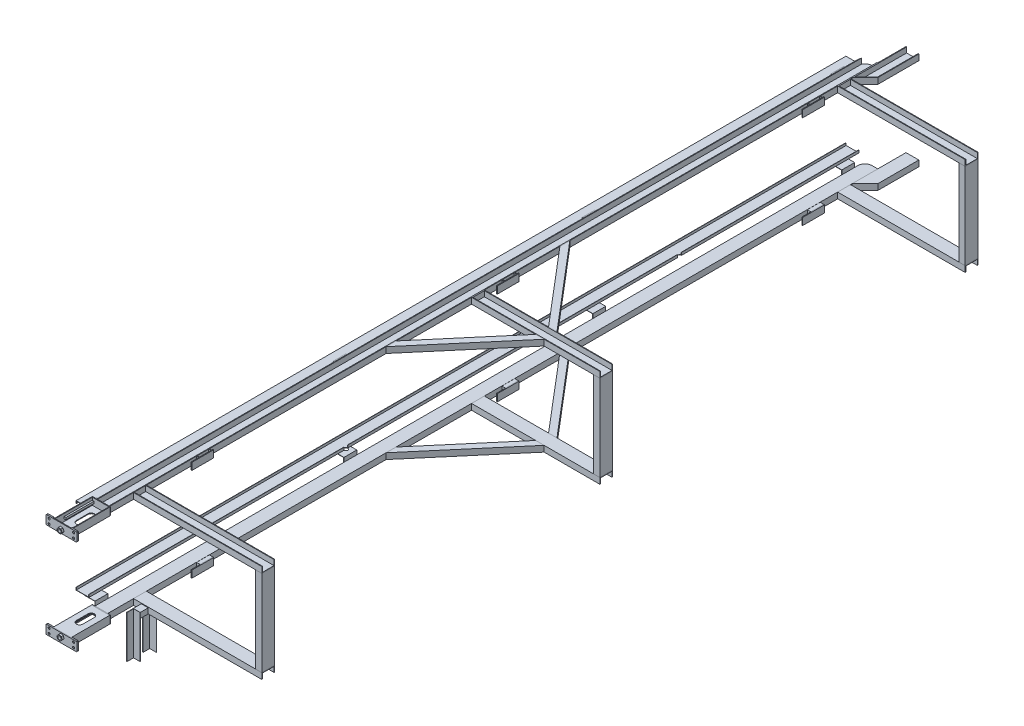
SolidWorks part; units mm, degrees
ref_plane "Front Plane" through (0, 0, 0) normal (0, 0, 1) x (1, 0, 0)
ref_plane "Top Plane" through (0, 0, 0) normal (0, 1, 0) x (1, 0, 0)
ref_plane "Right Plane" through (0, 0, 0) normal (1, 0, 0) x (0, 0, -1)
sketch "Sketch12" plane through (0, 0, 0) normal (0, 0, 1) x (1, 0, 0)
  line L0 (-50, 0) -> (50, 0)
  line L1 (-50, 0) -> (-50, 46)
  line L2 (50, 0) -> (50, 46)
  line L3 (-45, 5) -> (-45, 46)
  line L4 (-45, 5) -> (45, 5)
  line L5 (45, 5) -> (45, 46)
  line L6 (-50, 46) -> (-45, 46)
  line L7 (45, 46) -> (50, 46)
  point P2 (0, 0)
  dimension "D1" = 46
  dimension "D2" = 100
  dimension "D3" = 5
extrude "Boss-Extrude1" add sketch "Sketch12" along normal mid plane 6000
sketch "Sketch24" plane through (0, 46, 0) normal (0, 1, 0) x (1, 0, 0)
  line L0 (50, -2700) -> (1050, -2700)
  line L1 (50, -3000) -> (50, 3000) construction
  line L3 (1050, -2800) -> (50, -2800)
  line L4 (50, -2800) -> (50, -2700)
  line L5 (1050, -2800) -> (1050, -2700)
  line L6 (1050, -2700) -> (1050, 2184.4351) construction
  line L12 (45, -3000) -> (-45, -3000) construction
  line L13 (50, 2855.5299) -> (50, -2700) construction
  line L20 (50, -2700) -> (356.6139, -2700) construction
  line L21 (1050, -2700) -> (1050, -2197.7251) construction
  line L22 (50, -2700) -> (50, 1395.9752) construction
  line L23 (50, -65.672) -> (1050, -65.672)
  line L24 (50, -165.672) -> (1050, -165.672)
  line L25 (1050, -65.672) -> (1050, -165.672)
  line L26 (50, -165.672) -> (50, -65.672)
  line L27 (50, 2687.522) -> (1043.7553, 2687.522)
  line L28 (50, 2787.522) -> (1042.4967, 2787.522) construction
  line L29 (50, 2687.522) -> (50, 2787.522)
  line L30 (50, 2787.522) -> (1043.7553, 2787.522)
  line L31 (1043.7553, 2787.522) -> (1043.7553, 2687.522)
  dimension "D1" = 200
  dimension "D2" = 100
  dimension "D3" = 1000
  dimension "D6" = 100
extrude "Boss-Extrude10" add sketch "Sketch24" against normal blind 46 separate body
shell "Shell1" thickness 5
shell "Shell2" thickness 5
sketch "Sketch31" plane through (0, 46, 0) normal (0, 1, 0) x (1, 0, 0)
  line L0 (50, 2551.1384) -> (77.987, 2551.1384)
  line L1 (77.987, 2551.1384) -> (77.987, 2451.1384)
  line L2 (77.987, 2451.1384) -> (50, 2451.1384)
  line L4 (50, -3000) -> (50, 3000) construction
  line L5 (50, 2451.1384) -> (50, 2551.1384)
  dimension "D1" = 100
  dimension "D2" = 27.987
extrude "Boss-Extrude15" add sketch "Sketch31" against normal blind 45 separate body
shell "Shell4" thickness 5
sketch "Sketch33" plane through (77.987, 0, -5338.5198) normal (-1, 0, 0) x (0, 0, 1)
  line L9 (2787.3813, 1) -> (2957.3813, 1)
  line L10 (2787.3813, 1) -> (2787.3813, 56)
  line L11 (2787.3813, 56) -> (2957.3813, 56)
  line L12 (2957.3813, 1) -> (2957.3813, 56)
  dimension "D1" = 170
  dimension "D2" = 55
extrude "Boss-Extrude23" add sketch "Sketch33" against normal blind 6 separate body
pattern_linear "LPattern2" count 3 spacing 2380 along (0, 0, 1) of bodies 132 145
sketch "Sketch34" plane through (0, 0, 3000) normal (0, 0, 1) x (1, 0, 0)
  line L0 (-70, 0) -> (70, 0)
  line L1 (-50, 0) -> (50, 0) construction
  line L2 (-70, 0) -> (-70, 60)
  line L3 (0, 0) -> (0, 71.8206) construction
  line L4 (70, 0) -> (70, 60)
  line L10 (70, 60) -> (-70, 60)
  point P4 (0, 0)
  point P5 (0, 0)
  dimension "D1" = 140
  dimension "D2" = 60
extrude "Boss-Extrude25" add sketch "Sketch34" along normal blind 6 separate body
sketch "Sketch35" plane through (0, 0, 3006) normal (0, 0, 1) x (1, 0, 0)
  line L0 (70, 0) -> (70, 60) construction
  line L1 (-70, 0) -> (70, 0) construction
  line L2 (-70, 60) -> (-70, 0) construction
  line L3 (70, 0) -> (70, 60)
  line L4 (-70, 0) -> (70, 0)
  line L5 (-70, 60) -> (-70, 0)
  line L6 (-65, 60) -> (-65, 5)
  line L7 (-65, 5) -> (65, 5)
  line L8 (65, 5) -> (65, 60)
  line L9 (-70, 60) -> (-65, 60)
  line L10 (70, 60) -> (65, 60)
  dimension "D1" = 5
extrude "Boss-Extrude26" add sketch "Sketch35" along normal blind 300 separate body
sketch "Sketch36" plane through (0, 0, 3006) normal (0, 0, 1) x (1, 0, 0)
  line L0 (0, 0) -> (0, 40.4824) construction
  line L1 (-65, 5) -> (-65, 60) construction
  line L2 (-65, 39) -> (-52, 39)
  line L3 (-65, 39) -> (-65, 23)
  line L4 (-65, 23) -> (-52, 23)
  line L5 (-52, 39) -> (-52, 23)
  line L6 (52, 39) -> (52, 23)
  line L7 (65, 23) -> (52, 23)
  line L8 (65, 39) -> (65, 23)
  line L9 (65, 39) -> (52, 39)
  line L10 (65, 5) -> (-65, 5) construction
  dimension "D1" = 18
  dimension "D2" = 16
  dimension "D3" = 13
extrude "Boss-Extrude27" add sketch "Sketch36" along normal blind 220 separate body
sketch "Sketch37" plane through (0, 0, 3306) normal (0, 0, 1) x (1, 0, 0)
  line L0 (120, 0) -> (-120, 0)
  line L4 (0, 70) -> (0, 0) construction
  line L8 (-120, 70) -> (-120, 0)
  line L9 (120, 70) -> (120, 0)
  line L12 (-95.1007, 70) -> (-95.1007, 0) construction
  line L13 (-95.1007, 35) -> (-108.4029, 35) construction
  line L14 (-120, 70) -> (120, 70)
  circle A0 centre (-95.1007, 53.4578) radius 8
  circle A1 centre (-95.1007, 16.5422) radius 8
  circle A2 centre (95.1007, 16.5422) radius 8
  circle A3 centre (95.1007, 53.4578) radius 8
  point P7 (-120, 35)
  dimension "D4" = 16
  dimension "D1" = 240
  dimension "D2" = 70
extrude "Boss-Extrude28" add sketch "Sketch37" along normal blind 6 separate body
sketch "Sketch39" plane through (0, 0, 3306) normal (0, 0, -1) x (-1, 0, 0)
  line L0 (0, 0) -> (0, 26)
  circle A0 centre (0, 26) radius 13
  dimension "D2" = 26
  dimension "D1" = 26
extrude "Cut-Extrude3" cut sketch "Sketch39" against normal blind 6
sketch "Sketch43" plane through (0, 46, 0) normal (0, 1, 0) x (1, 0, 0)
  line L0 (50, 2900.0313) -> (50, 3220.0313)
  line L1 (50, -3000) -> (50, 3000) construction
  line L2 (50, 3220.0313) -> (150, 3220.0313)
  line L3 (150, 3220.0313) -> (150, 2900.0313)
  line L6 (50, 3000) -> (150, 3000) construction
  line L7 (50, 2900.0313) -> (150, 2900.0313) construction
  line L8 (150, 2900.0313) -> (50, 2800.0313)
  line L9 (50, 2900.0313) -> (50, 2800.0313)
  line L10 (45, 3000) -> (-45, 3000) construction
  dimension "D1" = 100
  dimension "D2" = 420
  dimension "D3" = 199.9687
  dimension "D4" = 100
extrude "Boss-Extrude31" add sketch "Sketch43" against normal blind 46 separate body
shell "Shell6" thickness 5
ref_plane "Plane1" through (0, -335, 0) normal (0, -1, 0) x (-1, 0, 0)
sketch "Sketch41" plane through (0, 5, 0) normal (0, 1, 0) x (1, 0, 0)
  line L0 (0, -3006) -> (0, -3249.3372) construction
  line L1 (65, -3006) -> (-65, -3006) construction
  line L2 (0, -3080) -> (0, -3170) construction
  line L3 (25, -3080) -> (25, -3170)
  line L4 (-25, -3080) -> (-25, -3170)
  line L5 (70, -3000) -> (-70, -3000) construction
  arc A0 (25, -3080) -> (-25, -3080) centre (0, -3080) ccw
  arc A1 (-25, -3170) -> (25, -3170) centre (0, -3170) ccw
  point P7 (0, -3125)
  point P13 (0, -3055)
  point P14 (0, -3195)
  dimension "D1" = 50
  dimension "D2" = 140
  dimension "D3" = 55
extrude "Cut-Extrude4" cut sketch "Sketch41" against normal blind 16
sketch "Sketch46" plane through (0, 5, 0) normal (0, 1, 0) x (1, 0, 0)
  line L0 (-50, -3000) -> (-50, 3000) construction
  line L1 (45, 3000) -> (-45, 3000) construction
  line L2 (-50, 2945.8864) -> (-52.794, 2945.8864)
  line L3 (-52.794, 2945.8864) -> (-52.794, 3001.4513)
  line L4 (-52.794, 3001.4513) -> (4.1136, 3001.4513)
  line L5 (4.1136, 3001.4513) -> (4.1136, 3000)
  arc A0 (4.1136, 3000) -> (-50, 2945.8864) centre (4.1136, 2945.8864) ccw
sketch "Sketch57" plane through (-70, 0, 0) normal (-1, 0, 0) x (0, 0, 1)
  line L0 (3306, 0) -> (3006, 0) construction
  line L1 (3306, 70) -> (3300, 70)
  line L2 (3306, 70) -> (3306, 0)
  line L3 (3306, 0) -> (3300, 0)
  line L4 (3300, 70) -> (3300, 0)
  dimension "D1" = 6
extrude "Boss-Extrude44" add sketch "Sketch57" along normal up to vertex (50 mm away) separate body
sketch "Sketch58" plane through (0, 0, 3306) normal (0, 0, 1) x (1, 0, 0)
  circle A0 centre (-95.1007, 53.4578) radius 8 construction
  circle A1 centre (-95.1007, 16.5422) radius 8 construction
  circle A2 centre (-95.1007, 53.4578) radius 8
  circle A3 centre (-95.1007, 16.5422) radius 8
extrude "Cut-Extrude6" cut sketch "Sketch58" against normal blind 50
shell "Shell7" thickness 5
extrude "Cut-Extrude7" cut sketch "Sketch46" along normal mid plane 153 contours A0 L2 L3 L4 L5
sketch "Sketch59" plane through (0, 0, 3306) normal (0, 0, -1) x (-1, 0, 0)
  line L1 (-120, 70) -> (-70, 70)
  line L2 (-120, 70) -> (-120, 0)
  line L3 (-120, 0) -> (-70, 0)
  line L4 (-70, 70) -> (-70, 0)
  circle A0 centre (-95.1007, 16.5422) radius 8 construction
  circle A1 centre (-95.1007, 53.4578) radius 8 construction
  circle A2 centre (-95.1007, 16.5422) radius 8
  circle A3 centre (-95.1007, 53.4578) radius 8
extrude "Boss-Extrude45" add sketch "Sketch59" along normal blind 6 separate body
fillet "Fillet1" radius 5 4 edges at (-120, 0, 3309) (-120, 70, 3309) (120, 70, 3309) (120, 0, 3309)
fillet "Fillet2" radius 5 2 edges at (120, 70, 3303) (120, 0, 3303)
fillet "Fillet3" radius 5 2 edges at (-120, 70, 3303) (-120, 0, 3303)
sketch "Sketch60" plane through (0, 46, 0) normal (0, 1, 0) x (1, 0, 0)
  line L0 (50, 523.1112) -> (550, -65.672)
  line L1 (50, -3000) -> (50, 3000) construction
  line L2 (1050, -65.672) -> (50, -65.672) construction
  line L3 (550, -65.672) -> (615.5964, -65.672)
  line L4 (615.5964, -65.672) -> (50, 600.3553)
  line L5 (50, 600.3553) -> (50, 523.1112)
  line L6 (1050, -115.672) -> (423.7069, -115.672) construction
  line L7 (1050, -160.672) -> (1050, -70.672) construction
  line L8 (50, -831.6993) -> (50, -754.4552)
  line L9 (615.5964, -165.672) -> (50, -831.6993)
  line L10 (550, -165.672) -> (615.5964, -165.672)
  line L11 (50, -754.4552) -> (550, -165.672)
  dimension "D1" = 50
extrude "Boss-Extrude46" add sketch "Sketch60" against normal up to surface (46 mm away) separate body up to face at (550, 0, 115.672)
mirror "Mirror1" about plane through (0, -335, 0) normal (0, -1, 0) of bodies 156 205 214 158 153 154 151 213 121 149 147 211 148 146 132 145 212 175 216 215
sketch "Sketch61" plane through (0, 0, 3312) normal (0, 0, 1) x (1, 0, 0)
  line L1 (12.158, 43.2116) -> (-8.8267, 45.135)
  line L2 (-8.8267, 45.135) -> (-20.9847, 27.9234)
  line L3 (-20.9847, 27.9234) -> (-12.158, 8.7884)
  line L4 (-12.158, 8.7884) -> (8.8267, 6.865)
  line L5 (8.8267, 6.865) -> (20.9847, 24.0766)
  line L6 (20.9847, 24.0766) -> (12.158, 43.2116)
  line L7 (-20.5282, -691.2406) -> (-14.3859, -711.3982)
  line L8 (-14.3859, -711.3982) -> (6.1423, -716.1576)
  line L9 (6.1423, -716.1576) -> (20.5282, -700.7594)
  line L10 (20.5282, -700.7594) -> (14.3859, -680.6018)
  line L11 (14.3859, -680.6018) -> (-6.1423, -675.8424)
  line L12 (-6.1423, -675.8424) -> (-20.5282, -691.2406)
  circle A0 centre (0, 26) radius 18.2495 construction
  circle A1 centre (0, 26) radius 13
  circle A2 centre (0, -696) radius 13 construction
  circle A3 centre (0, -696) radius 13
  circle A4 centre (0, -696) radius 18.2495 construction
extrude "Boss-Extrude47" add sketch "Sketch61" along normal blind 15 separate body
sketch "Sketch63" plane through (0, 0, 0) normal (0, -1, 0) x (1, 0, 0)
  line L0 (50, -2687.522) -> (1043.7553, -2687.522) construction
  line L1 (1043.7553, -2787.522) -> (993.7553, -2787.522)
  line L2 (1043.7553, -2787.522) -> (1043.7553, -2687.522)
  line L3 (1043.7553, -2687.522) -> (993.7553, -2687.522)
  line L4 (993.7553, -2787.522) -> (993.7553, -2687.522)
  line L5 (50, 165.672) -> (1050, 165.672) construction
  line L6 (1050, 65.672) -> (1000, 65.672)
  line L7 (1050, 65.672) -> (1050, 165.672)
  line L8 (1050, 165.672) -> (1000, 165.672)
  line L9 (1000, 65.672) -> (1000, 165.672)
  line L10 (50, 2800) -> (1050, 2800) construction
  line L11 (1050, 2700) -> (1000, 2700)
  line L12 (1050, 2700) -> (1050, 2800)
  line L13 (1050, 2800) -> (1000, 2800)
  line L14 (1000, 2700) -> (1000, 2800)
  dimension "D1" = 50
extrude "Boss-Extrude48" add sketch "Sketch63" along normal up to surface (670 mm away) separate body up to face at (550, -670, 115.672)
sketch "Sketch64" plane through (0, 0, 0) normal (0, 0, 1) x (1, 0, 0)
  line L0 (993.7553, -335) -> (-100, -335) construction
  line L1 (993.7553, -670) -> (993.7553, 0) construction
  line L2 (-100, -335) -> (-100, -35) construction
  line L3 (-100, -53) -> (-100, -35)
  line L4 (-100, -35) -> (-196, -35)
  line L5 (-196, -35) -> (-196, -53)
  line L6 (-98, -53) -> (-98, -33)
  line L7 (-98, -33) -> (-198, -33)
  line L8 (-198, -33) -> (-198, -53)
  line L9 (-98, -53) -> (-100, -53)
  line L10 (-196, -53) -> (-198, -53)
  line L11 (-70, 0) -> (-70, 70) construction
  dimension "D1" = 300
  dimension "D3" = 100
  dimension "D4" = 30
  dimension "D5" = 20
  dimension "D2" = 2
extrude "Boss-Extrude49" add sketch "Sketch64" along normal mid plane 6000 separate body
sketch "Sketch65" plane through (0, 0, 3000) normal (0, 0, 1) x (1, 0, 0)
  line L0 (-50, 29.4046) -> (-50, 0)
  line L1 (-50, 0) -> (-50, -33)
  line L2 (-50, -33) -> (-135.1481, -33)
  line L3 (-98, -33) -> (-198, -33) construction
  line L4 (-52, 29.4046) -> (-52, 0)
  line L5 (-52, 0) -> (-52, -31)
  line L6 (-52, -31) -> (-135.1481, -31)
  line L7 (-50, 29.4046) -> (-52, 29.4046)
  line L8 (-135.1481, -31) -> (-135.1481, -33)
  dimension "D1" = 2
extrude "Boss-Extrude50" add sketch "Sketch65" against normal blind 100 separate body
pattern_linear "LPattern3" count 4 spacing 1940 along (0, 0, -1) of bodies 245
mirror "Mirror2" about plane through (0, -335, 0) normal (0, -1, 0) of bodies 248 244 247 245 246
sketch "Sketch66" plane through (0, -33, 0) normal (0, 1, 0) x (1, 0, 0)
  line L0 (-148, -3000) -> (-148, -996.97) construction
  line L1 (-98, -3000) -> (-198, -3000) construction
  line L2 (-148, -996.97) -> (-98, -996.97) construction
  line L3 (-98, -3000) -> (-98, 3000) construction
  line L4 (-98, 3000) -> (-98, 1603.03) construction
  line L5 (-98, 3000) -> (-198, 3000) construction
  circle A0 centre (-98, -996.97) radius 15
  circle A1 centre (-98, 1603.03) radius 15
  dimension "D1" = 30
  dimension "D3" = 30
  dimension "D4" = 1396.97
  dimension "D2" = 2003.03
extrude "Cut-Extrude8" cut sketch "Sketch66" against normal blind 1459
sketch "Sketch67" plane through (0, -675, 0) normal (0, -1, 0) x (1, 0, 0)
  line L0 (50, 2705) -> (50, 2795) construction
  line L1 (110.5, 2734.3365) -> (164.727, 2734.3365)
  line L2 (110.5, 2734.3365) -> (110.5, 2788.5635)
  line L5 (50, 2795) -> (1050, 2795) construction
  line L6 (113.5, 2737.3365) -> (164.727, 2737.3365)
  line L7 (113.5, 2737.3365) -> (113.5, 2788.5635)
  line L8 (113.5, 2788.5635) -> (110.5, 2788.5635)
  line L9 (164.727, 2737.3365) -> (164.727, 2734.3365)
  line L10 (50, 2887.45) -> (132.3002, 2887.45) construction
  line L11 (50, 3000) -> (50, -3000) construction
  line L12 (113.5, 2863.3365) -> (164.727, 2863.3365)
  line L13 (110.5, 2860.3365) -> (164.727, 2860.3365)
  line L14 (113.5, 2914.5635) -> (110.5, 2914.5635)
  line L15 (164.727, 2863.3365) -> (164.727, 2860.3365)
  line L16 (113.5, 2863.3365) -> (113.5, 2914.5635)
  line L17 (110.5, 2860.3365) -> (110.5, 2914.5635)
  point P8 (110.5, 2761.45)
  dimension "D1" = 60.5
  dimension "D2" = 33.55
  dimension "D4" = 126
  dimension "D3" = 3
extrude "Boss-Extrude51" add sketch "Sketch67" along normal blind 331.8 separate body
sketch "Sketch68" plane through (0, 0, 2800) normal (0, 0, 1) x (1, 0, 0)
  line L0 (110.5, -675) -> (164.727, -675) construction
  line L1 (110.5, -675) -> (164.727, -675)
  line L2 (110.5, -675) -> (110.5, -716)
  line L3 (50, -716) -> (1050, -716) construction
  line L4 (110.5, -716) -> (164.727, -716)
  line L5 (164.727, -716) -> (164.727, -675)
extrude "Boss-Extrude52" add sketch "Sketch68" along normal up to surface (60.3365 mm away) separate body up to face at (137.6135, -840.9, 2860.3365)
